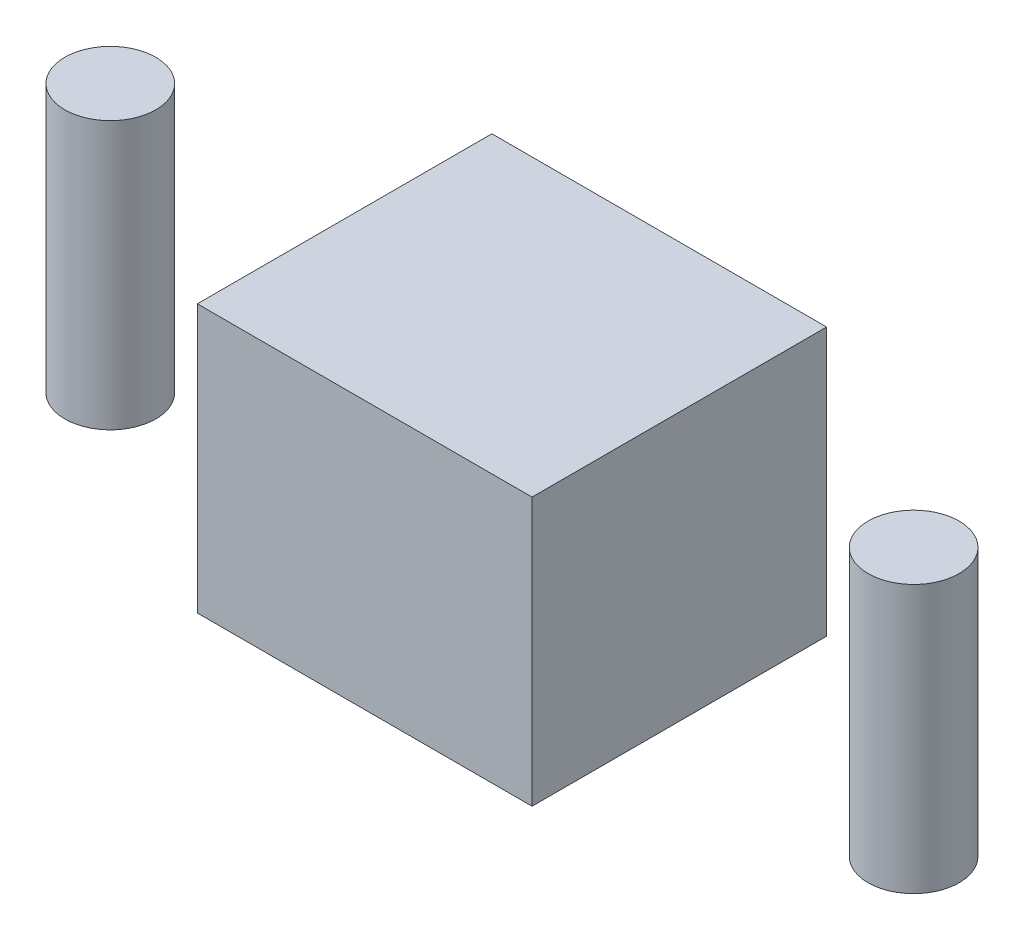
SolidWorks part; units mm, degrees
ref_plane "Front Plane" through (0, 0, 0) normal (0, 0, 1) x (1, 0, 0)
ref_plane "Top Plane" through (0, 0, 0) normal (0, 1, 0) x (1, 0, 0)
ref_plane "Right Plane" through (0, 0, 0) normal (1, 0, 0) x (0, 0, -1)
sketch "Sketch2" plane through (0, 0, 0) normal (0, 1, 0) x (1, 0, 0)
  line L5 (-6.25, -5.5) -> (6.25, -5.5)
  line L6 (-6.25, -5.5) -> (-6.25, 5.5)
  line L7 (-6.25, 5.5) -> (6.25, 5.5)
  line L8 (6.25, -5.5) -> (6.25, 5.5)
  line L9 (-6.25, -5.5) -> (6.25, 5.5) construction
  line L10 (-6.25, 5.5) -> (6.25, -5.5) construction
  circle A0 centre (15, 0) radius 1.7
  circle A1 centre (-15, 0) radius 1.7
  point P0 (0, 0)
extrude "Boss-Extrude1" add sketch "Sketch2" along normal blind 10
